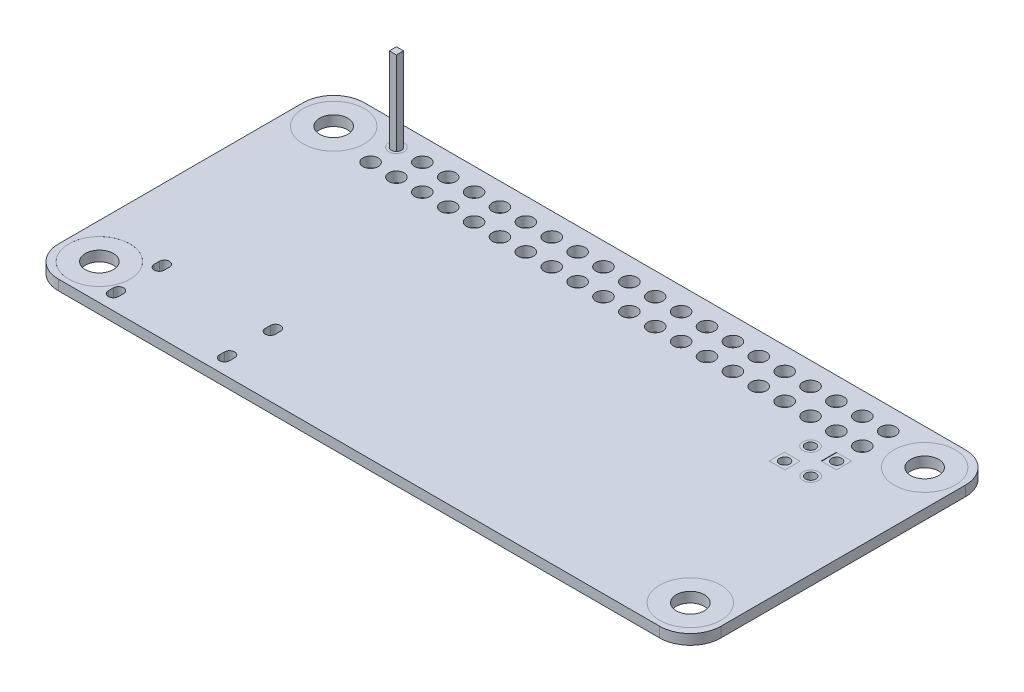
SolidWorks part; units mm, degrees
ref_plane "Front Plane" through (0, 0, 0) normal (0, 0, 1) x (1, 0, 0)
ref_plane "Top Plane" through (0, 0, 0) normal (0, 1, 0) x (1, 0, 0)
ref_plane "Right Plane" through (0, 0, 0) normal (1, 0, 0) x (0, 0, -1)
sketch "Sketch1" plane through (0, 0, 0) normal (0, 1, 0) x (1, 0, 0)
  line L0 (-27.4768, 39.9178) -> (-27.4768, -37.6558) construction
  line L1 (-29.5, -15) -> (29.5, -15)
  line L2 (-32.5, -12) -> (-32.5, 12)
  line L3 (-29.5, 15) -> (29.5, 15)
  line L4 (32.5, -12) -> (32.5, 12)
  line L5 (-32.5, -15) -> (32.5, 15) construction
  line L6 (-32.5, 15) -> (32.5, -15) construction
  line L7 (0, 0) -> (0, 39.9178) construction
  line L9 (-25.5, 14.1112) -> (25.5, 14.1112) construction
  line L10 (-25.5, 14.1112) -> (-25.5, 8.9112) construction
  line L11 (-25.5, 8.9112) -> (25.5, 8.9112) construction
  line L12 (25.5, 14.1112) -> (25.5, 8.9112) construction
  line L13 (23.38, 6.9577) -> (24.88, 6.9577)
  line L14 (23.38, 6.9577) -> (23.38, 8.4577)
  line L15 (23.38, 8.4577) -> (24.88, 8.4577)
  line L16 (24.88, 6.9577) -> (24.88, 8.4577)
  line L17 (23.38, 6.9577) -> (24.88, 8.4577) construction
  line L18 (23.38, 8.4577) -> (24.88, 6.9577) construction
  line L19 (20.8606, 4.4177) -> (22.3606, 4.4177)
  line L20 (20.8606, 4.4177) -> (20.8606, 5.9177)
  line L21 (20.8606, 5.9177) -> (22.3606, 5.9177)
  line L22 (22.3606, 4.4177) -> (22.3606, 5.9177)
  line L23 (20.8606, 4.4177) -> (22.3606, 5.9177) construction
  line L24 (20.8606, 5.9177) -> (22.3606, 4.4177) construction
  arc A0 (-32.5, 12) -> (-29.5, 15) centre (-29.5, 12) cw
  arc A1 (-29.5, -15) -> (-32.5, -12) centre (-29.5, -12) cw
  arc A2 (29.5, -15) -> (32.5, -12) centre (29.5, -12) ccw
  arc A3 (29.5, 15) -> (32.5, 12) centre (29.5, 12) cw
  circle A4 centre (-29, 11.5) radius 3
  circle A5 centre (-29, -11.5) radius 3
  circle A6 centre (29, -11.5) radius 3
  circle A7 centre (-24.13, 12.7877) radius 0.75
  circle A8 centre (-21.59, 12.7877) radius 0.75
  circle A9 centre (-19.05, 12.7877) radius 0.75
  circle A10 centre (-16.51, 12.7877) radius 0.75
  circle A11 centre (-13.97, 12.7877) radius 0.75
  circle A12 centre (-11.43, 12.7877) radius 0.75
  circle A13 centre (-8.89, 12.7877) radius 0.75
  circle A14 centre (-6.35, 12.7877) radius 0.75
  circle A15 centre (-3.81, 12.7877) radius 0.75
  circle A16 centre (-1.27, 12.7877) radius 0.75
  circle A17 centre (1.27, 12.7877) radius 0.75
  circle A18 centre (3.81, 12.7877) radius 0.75
  circle A19 centre (6.35, 12.7877) radius 0.75
  circle A20 centre (8.89, 12.7877) radius 0.75
  circle A21 centre (11.43, 12.7877) radius 0.75
  circle A22 centre (13.97, 12.7877) radius 0.75
  circle A23 centre (16.51, 12.7877) radius 0.75
  circle A24 centre (19.05, 12.7877) radius 0.75
  circle A25 centre (21.59, 12.7877) radius 0.75
  circle A26 centre (24.13, 12.7877) radius 0.75
  circle A27 centre (-21.59, 10.2477) radius 0.75
  circle A28 centre (-19.05, 10.2477) radius 0.75
  circle A29 centre (-16.51, 10.2477) radius 0.75
  circle A30 centre (-13.97, 10.2477) radius 0.75
  circle A31 centre (-11.43, 10.2477) radius 0.75
  circle A32 centre (-8.89, 10.2477) radius 0.75
  circle A33 centre (-6.35, 10.2477) radius 0.75
  circle A34 centre (-3.81, 10.2477) radius 0.75
  circle A35 centre (-1.27, 10.2477) radius 0.75
  circle A36 centre (1.27, 10.2477) radius 0.75
  circle A37 centre (3.81, 10.2477) radius 0.75
  circle A38 centre (6.35, 10.2477) radius 0.75
  circle A39 centre (8.89, 10.2477) radius 0.75
  circle A40 centre (11.43, 10.2477) radius 0.75
  circle A41 centre (13.97, 10.2477) radius 0.75
  circle A42 centre (16.51, 10.2477) radius 0.75
  circle A43 centre (19.05, 10.2477) radius 0.75
  circle A44 centre (21.59, 10.2477) radius 0.75
  circle A45 centre (24.13, 10.2477) radius 0.75
  circle A46 centre (-24.13, 10.2477) radius 0.75
  circle A47 centre (21.59, 7.7077) radius 0.75
  circle A48 centre (24.1506, 5.1677) radius 0.75
  circle A49 centre (29, 11.5) radius 3
  point P0 (0, 0)
  point P32 (0, 8.9112)
  point P117 (24.13, 7.7077)
  point P122 (21.6106, 5.1677)
  dimension "D3" = 3
  dimension "D4" = 51
  dimension "D5" = 6
  dimension "D11" = 1.5
  dimension "D12" = 2
  dimension "D15" = 1.5
  dimension "D16" = 1.5
  dimension "D27" = 6
  dimension "D28" = 6
  dimension "D1" = 65
  dimension "D2" = 30
  dimension "D6" = 23
  dimension "D7" = 29
  dimension "D8" = 3.5
  dimension "D9" = 5.2
  dimension "D10" = 29
  dimension "D13" = 1.27
  dimension "D14" = 20
  dimension "D17" = 2.54
  dimension "D18" = 2.54
  dimension "D19" = 2.54
  dimension "D20" = 2.54
  dimension "D21" = 2.54
  dimension "D22" = 2.54
  dimension "D23" = 1.5
  dimension "D24" = 1.5
  dimension "D25" = 1.5
  dimension "D26" = 1.5
extrude "Boss-Extrude1" add sketch "Sketch1" along normal blind 1
sketch "Sketch2" plane through (0, 0, 0) normal (0, 1, 0) x (1, 0, 0)
  circle A0 centre (-24.13, 12.7877) radius 0.75 construction
  circle A1 centre (-24.13, 12.7877) radius 0.75
  circle A3 centre (-24.13, 12.7877) radius 0.5
  dimension "D1" = 1
extrude "Boss-Extrude2" add sketch "Sketch2" along normal blind 1 separate body
sketch "Sketch6" plane through (0, 1, 0) normal (0, 1, 0) x (1, 0, 0)
  line L0 (-23.78, 12.4377) -> (-23.78, 13.1377)
  line L1 (-23.78, 12.4377) -> (-24.48, 12.4377)
  line L2 (-23.78, 13.1377) -> (-24.48, 13.1377)
  line L3 (-24.48, 12.4377) -> (-24.48, 13.1377)
  line L4 (-23.78, 12.4377) -> (-24.48, 13.1377) construction
  line L5 (-23.78, 13.1377) -> (-24.48, 12.4377) construction
  circle A0 centre (-24.13, 12.7877) radius 0.5 construction
  point P1 (-24.13, 12.7877)
  dimension "D1" = 0.7
extrude "Boss-Extrude5" add sketch "Sketch6" along normal blind 8.2 and the other way blind 3
pattern_linear "LPattern2" [suppressed] count 20 spacing 2.54 count 2 spacing 2.54
sketch "Sketch3" plane through (0, 0, 0) normal (0, 1, 0) x (1, 0, 0)
  line L1 (20.8194, 4.4177) -> (22.3606, 4.4177)
  line L2 (20.8194, 4.4177) -> (20.8194, 5.9177)
  line L3 (20.8194, 5.9177) -> (22.3606, 5.9177)
  line L4 (22.3606, 4.4177) -> (22.3606, 5.9177)
  line L5 (20.8194, 4.4177) -> (22.3606, 5.9177) construction
  line L6 (20.8194, 5.9177) -> (22.3606, 4.4177) construction
  line L7 (23.4212, 6.9577) -> (24.88, 6.9577)
  line L8 (23.4212, 6.9577) -> (23.4212, 8.4577)
  line L9 (23.4212, 8.4577) -> (24.88, 8.4577)
  line L10 (24.88, 6.9577) -> (24.88, 8.4577)
  line L11 (23.4212, 6.9577) -> (24.88, 8.4577) construction
  line L12 (23.4212, 8.4577) -> (24.88, 6.9577) construction
  circle A0 centre (21.59, 7.7077) radius 0.75
  circle A1 centre (21.59, 7.7077) radius 0.5
  circle A2 centre (24.1506, 5.1677) radius 0.75
  circle A3 centre (24.1506, 5.1677) radius 0.5
  circle A4 centre (24.1506, 7.7077) radius 0.5
  circle A5 centre (21.59, 5.1677) radius 0.5
  dimension "D1" = 1
  dimension "D2" = 1
  dimension "D3" = 1
  dimension "D4" = 1
extrude "Boss-Extrude3" add sketch "Sketch3" along normal blind 1 separate body
sketch "Sketch4" plane through (0, 0, 0) normal (0, 1, 0) x (1, 0, 0)
  circle A0 centre (-29, 11.5) radius 3
  circle A1 centre (-29, 11.5) radius 1.375
  dimension "D1" = 2.75
extrude "Boss-Extrude4" add sketch "Sketch4" along normal blind 1 separate body
mirror "Mirror1" about plane through (0, 0, 0) normal (1, 0, 0) of bodies 147
mirror "Mirror2" about plane through (0, 0, 0) normal (0, 0, 1) of bodies 147 148
sketch "Sketch5" plane through (0, 0, 0) normal (0, -1, 0) x (1, 0, 0)
  line L0 (-25.5788, 13.0395) -> (-25.5788, 13.5395) construction
  line L1 (-26.0788, 13.0395) -> (-26.0788, 13.5395)
  line L2 (-25.0788, 13.0395) -> (-25.0788, 13.5395)
  line L3 (-14.6788, 13.0395) -> (-14.6788, 13.5395) construction
  line L4 (-15.1788, 13.0395) -> (-15.1788, 13.5395)
  line L5 (-14.1788, 13.0395) -> (-14.1788, 13.5395)
  line L6 (-14.6788, 8.5395) -> (-14.6788, 9.0395) construction
  line L7 (-15.1788, 8.5395) -> (-15.1788, 9.0395)
  line L8 (-14.1788, 8.5395) -> (-14.1788, 9.0395)
  line L9 (-25.5788, 8.5395) -> (-25.5788, 9.0395) construction
  line L10 (-26.0788, 8.5395) -> (-26.0788, 9.0395)
  line L11 (-25.0788, 8.5395) -> (-25.0788, 9.0395)
  arc A0 (-26.0788, 13.0395) -> (-25.0788, 13.0395) centre (-25.5788, 13.0395) ccw
  arc A1 (-25.0788, 13.5395) -> (-26.0788, 13.5395) centre (-25.5788, 13.5395) ccw
  arc A2 (-15.1788, 13.0395) -> (-14.1788, 13.0395) centre (-14.6788, 13.0395) ccw
  arc A3 (-14.1788, 13.5395) -> (-15.1788, 13.5395) centre (-14.6788, 13.5395) ccw
  arc A4 (-15.1788, 8.5395) -> (-14.1788, 8.5395) centre (-14.6788, 8.5395) ccw
  arc A5 (-14.1788, 9.0395) -> (-15.1788, 9.0395) centre (-14.6788, 9.0395) ccw
  arc A6 (-26.0788, 8.5395) -> (-25.0788, 8.5395) centre (-25.5788, 8.5395) ccw
  arc A7 (-25.0788, 9.0395) -> (-26.0788, 9.0395) centre (-25.5788, 9.0395) ccw
  point P2 (-25.5788, 13.2895)
  point P11 (-14.6788, 13.2895)
  point P18 (-14.6788, 8.7895)
  point P25 (-25.5788, 8.7895)
  dimension "D2" = 0.5
  dimension "D1" = 0.5
  dimension "D3" = 2
extrude "Cut-Extrude1" cut sketch "Sketch5" against normal blind 1
